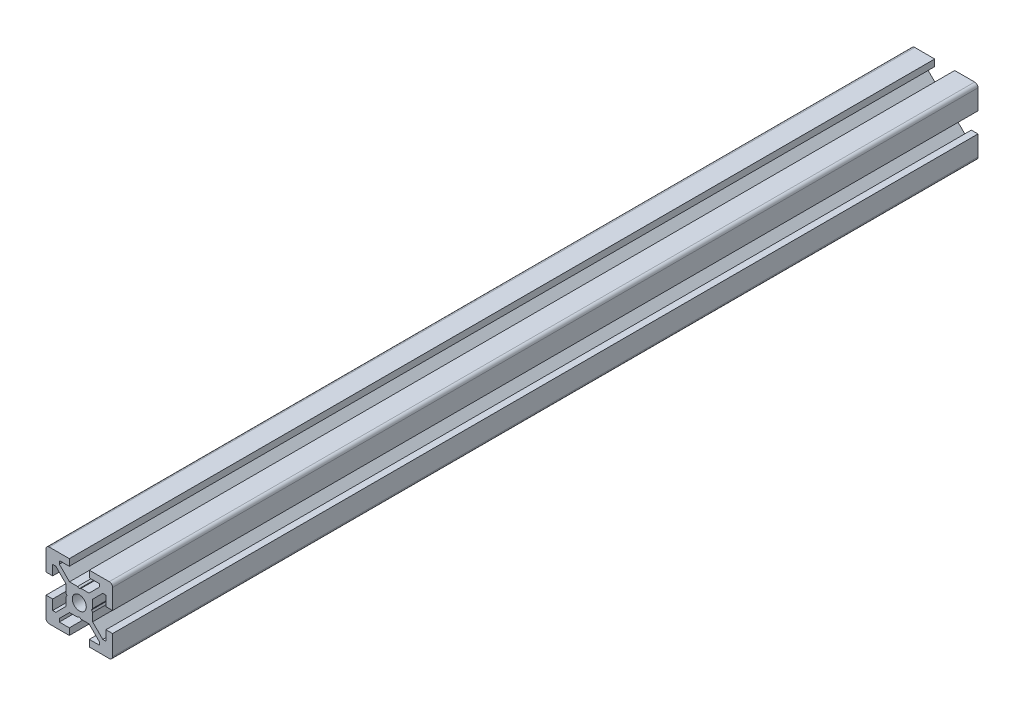
SolidWorks part; units mm, degrees
material "2014 合金"
ref_plane "正面" through (0, 0, 0) normal (0, 0, 1) x (1, 0, 0)
ref_plane "平面" through (0, 0, 0) normal (0, 1, 0) x (1, 0, 0)
ref_plane "右側面" through (0, 0, 0) normal (1, 0, 0) x (0, 0, -1)
ref_plane "平面1" through (0, 0, 0) normal (0, 0, 1) x (1, 0, 0)
sketch "ｽｹｯﾁ1" plane through (0, 0, 0) normal (0, 0, 1) x (1, 0, 0)
  line L0 (-10, -3) -> (-10, -9)
  line L1 (-9, -10) -> (-3, -10)
  line L2 (-3, -10) -> (-3, -8)
  line L3 (-3, -8) -> (-6, -8)
  line L4 (-6, -8) -> (-6, -7.0607)
  line L5 (-6, -7.0607) -> (-2.9393, -4)
  line L6 (-2.9393, -4) -> (-0.5196, -4)
  line L7 (-0.5196, -4) -> (0, -3.7)
  line L8 (0, -3.7) -> (0.5196, -4)
  line L9 (0.5196, -4) -> (2.9393, -4)
  line L10 (2.9393, -4) -> (6, -7.0607)
  line L11 (6, -7.0607) -> (6, -8)
  line L12 (6, -8) -> (3, -8)
  line L13 (3, -8) -> (3, -10)
  line L14 (3, -10) -> (9, -10)
  line L15 (10, -9) -> (10, -3)
  line L16 (10, -3) -> (8, -3)
  line L17 (8, -3) -> (8, -6)
  line L18 (8, -6) -> (7.0607, -6)
  line L19 (7.0607, -6) -> (4, -2.9393)
  line L20 (4, -2.9393) -> (4, -0.5196)
  line L21 (4, -0.5196) -> (3.7, 0)
  line L22 (3.7, 0) -> (4, 0.5196)
  line L23 (4, 0.5196) -> (4, 2.9393)
  line L24 (4, 2.9393) -> (7.0607, 6)
  line L25 (7.0607, 6) -> (8, 6)
  line L26 (8, 6) -> (8, 3)
  line L27 (8, 3) -> (10, 3)
  line L28 (10, 3) -> (10, 9)
  line L29 (9, 10) -> (3, 10)
  line L30 (3, 10) -> (3, 8)
  line L31 (3, 8) -> (6, 8)
  line L32 (6, 8) -> (6, 7.0607)
  line L33 (6, 7.0607) -> (2.9393, 4)
  line L34 (2.9393, 4) -> (0.5196, 4)
  line L35 (0.5196, 4) -> (0, 3.7)
  line L36 (0, 3.7) -> (-0.5196, 4)
  line L37 (-0.5196, 4) -> (-2.9393, 4)
  line L38 (-2.9393, 4) -> (-6, 7.0607)
  line L39 (-6, 7.0607) -> (-6, 8)
  line L40 (-6, 8) -> (-3, 8)
  line L41 (-3, 8) -> (-3, 10)
  line L42 (-3, 10) -> (-9, 10)
  line L43 (-10, 9) -> (-10, 3)
  line L44 (-10, 3) -> (-8, 3)
  line L45 (-8, 3) -> (-8, 6)
  line L46 (-8, 6) -> (-7.0607, 6)
  line L47 (-7.0607, 6) -> (-4, 2.9393)
  line L48 (-4, 2.9393) -> (-4, 0.5196)
  line L49 (-4, 0.5196) -> (-3.7, 0)
  line L50 (-3.7, 0) -> (-4, -0.5196)
  line L51 (-4, -0.5196) -> (-4, -2.9393)
  line L52 (-4, -2.9393) -> (-7.0607, -6)
  line L53 (-7.0607, -6) -> (-8, -6)
  line L54 (-8, -6) -> (-8, -3)
  line L55 (-8, -3) -> (-10, -3)
  arc A0 (-10, -9) -> (-9, -10) centre (-9, -9) ccw
  arc A1 (9, -10) -> (10, -9) centre (9, -9) ccw
  arc A2 (10, 9) -> (9, 10) centre (9, 9) ccw
  arc A3 (-9, 10) -> (-10, 9) centre (-9, 9) ccw
extrude "ﾎﾞｽ - 押し出し1" add sketch "ｽｹｯﾁ1" against normal blind 260
ref_plane "平面2" through (0, 0, 0) normal (1, 0, 0) x (0, 0, -1)
sketch "ｽｹｯﾁ2" plane through (0, 0, 0) normal (1, 0, 0) x (0, 0, -1)
  line L0 (0, 0) -> (0, 2.1)
  line L1 (0, 2.1) -> (260, 2.1)
  line L2 (260, 2.1) -> (260, 0)
  line L3 (260, 0) -> (0, 0)
  line L4 (260, 0) -> (0, 0) construction
revolve "ｶｯﾄ - 回転1" cut sketch "ｽｹｯﾁ2" angle 360 about L4
